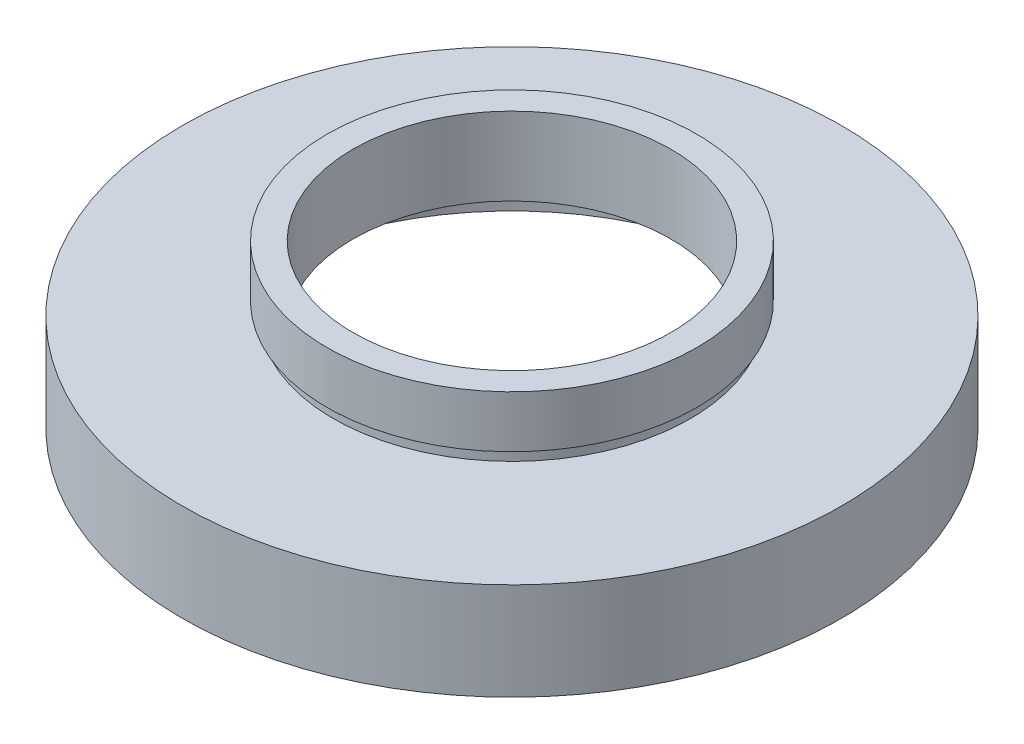
SolidWorks part; units mm, degrees
ref_plane "前视基准面" through (0, 0, 0) normal (0, 0, 1) x (1, 0, 0)
ref_plane "上视基准面" through (0, 0, 0) normal (0, 1, 0) x (1, 0, 0)
ref_plane "右视基准面" through (0, 0, 0) normal (1, 0, 0) x (0, 0, -1)
sketch "草图1" plane through (0, 0, 0) normal (0, 0, 1) x (1, 0, 0)
  line L0 (0, 16.886) -> (0, -24.4878) construction
  line L1 (20.5, 0) -> (20.5, 5.5)
  line L2 (12.25, 6.5) -> (21.1, 6.5)
  line L3 (12.25, 6.5) -> (12.25, 12.5)
  line L4 (12.25, 12.5) -> (14.25, 12.5)
  line L5 (14.25, 12.5) -> (14.25, 8.5)
  line L6 (14.25, 8.5) -> (13.75, 8.5)
  line L7 (13.75, 8.5) -> (13.75, 7.5)
  line L8 (13.75, 7.5) -> (25.4, 7.5)
  line L9 (25.4, 7.5) -> (25.4, 0)
  line L10 (25.4, 0) -> (20.5, 0)
  line L11 (20.5, 5.5) -> (21.1, 5.5)
  line L12 (21.1, 5.5) -> (21.1, 6.5)
  line L13 (0, 0) -> (3.4668, 0) construction
  point P4 (22.95, 0)
  dimension "D1" = 12.25
  dimension "D2" = 14.25
  dimension "D3" = 13.75
  dimension "D4" = 20.5
  dimension "D5" = 21.1
  dimension "D6" = 25.4
  dimension "D7" = 12.5
  dimension "D8" = 7.5
  dimension "D9" = 1
  dimension "D10" = 5.5
  dimension "D11" = 1
revolve "旋转1" add sketch "草图1" angle 360 about L0
cosmetic thread "装饰螺纹线1" parameters "D2"=27.5
cosmetic thread "装饰螺纹线2" parameters "D2"=25.5
cosmetic thread "装饰螺纹线3" parameters "D2"=42
